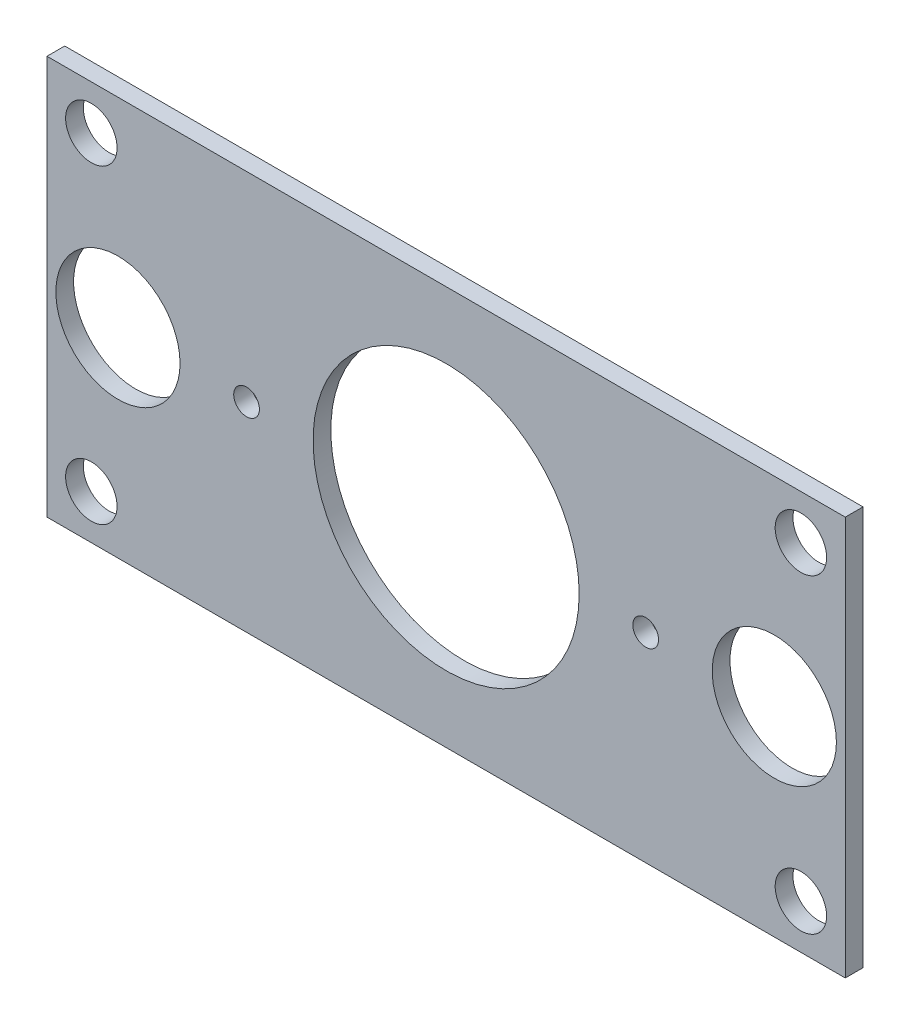
SolidWorks part; units mm, degrees
ref_plane "Front" through (0, 0, 0) normal (0, 0, 1) x (1, 0, 0)
ref_plane "Top" through (0, 0, 0) normal (0, 1, 0) x (1, 0, 0)
ref_plane "Right" through (0, 0, 0) normal (1, 0, 0) x (0, 0, -1)
sketch "草图1" plane through (0, 0, 0) normal (0, 0, 1) x (1, 0, 0)
  line L1 (-45, 22.5) -> (45, 22.5)
  line L2 (-45, 22.5) -> (-45, -22.5)
  line L3 (-45, -22.5) -> (45, -22.5)
  line L4 (45, 22.5) -> (45, -22.5)
  circle A0 centre (-40, 17.5) radius 2.9
  circle A1 centre (-40, -17.5) radius 2.9
  circle A2 centre (40, 17.5) radius 2.9
  circle A3 centre (40, -17.5) radius 2.9
  circle A4 centre (22.5, 0) radius 1.45
  circle A5 centre (-22.5, 0) radius 1.45
  circle A6 centre (0, 0) radius 15
  circle A7 centre (-37, 0) radius 7
  circle A8 centre (37, 0) radius 7
  point P0 (0, 0)
  point P10 (0, 0)
  point P15 (0, 0)
extrude "凸台-拉伸2" add sketch "草图1" against normal blind 2
